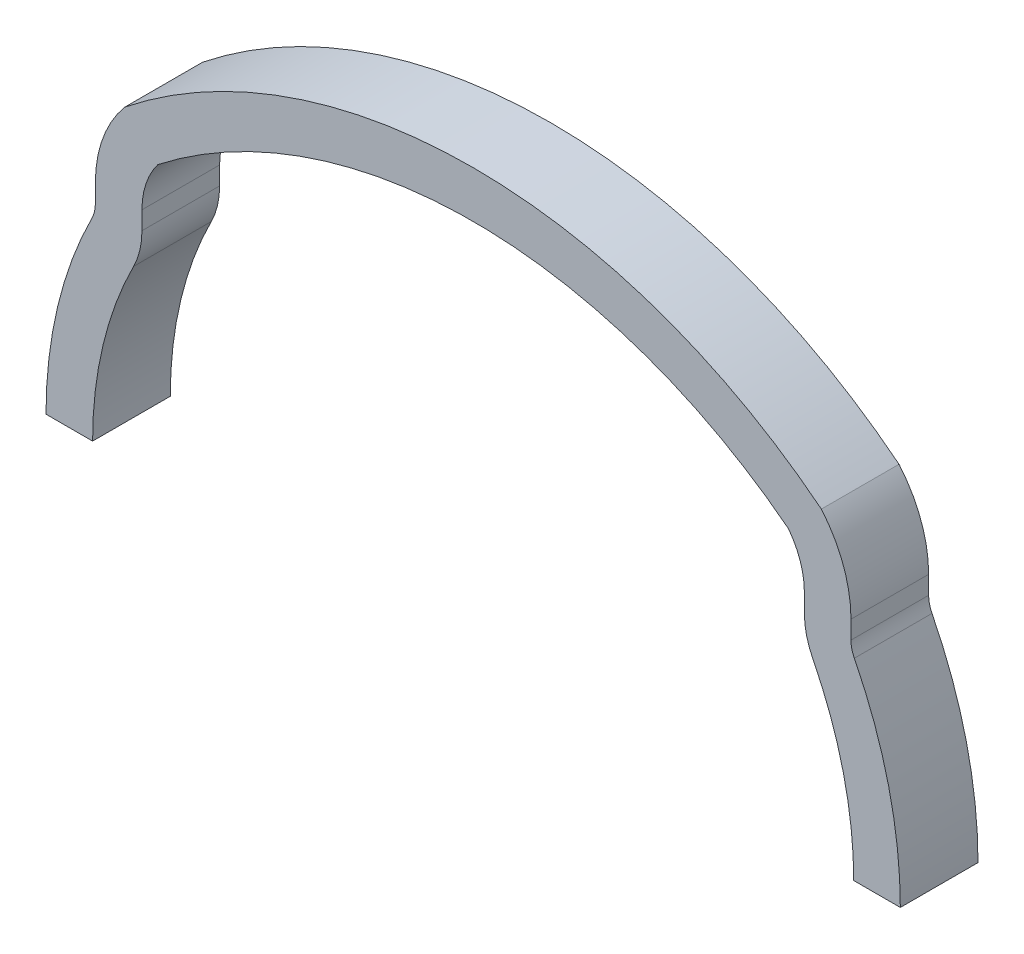
SolidWorks part; units mm, degrees
ref_plane "Front Plane" through (0, 0, 0) normal (0, 0, 1) x (1, 0, 0)
ref_plane "Top Plane" through (0, 0, 0) normal (0, 1, 0) x (1, 0, 0)
ref_plane "Right Plane" through (0, 0, 0) normal (1, 0, 0) x (0, 0, -1)
sketch "Sketch1" plane through (0, 0, 0) normal (0, 0, 1) x (1, 0, 0)
  line L1 (0, 0) -> (-38.2853, 0) construction
  line L2 (0, 0) -> (0, 65.2519) construction
  line L4 (-21, 16.3042) -> (-19.2879, 14.282) construction
  line L5 (-24.3231, 14.4853) -> (-24.3231, 13.3171)
  line L8 (-21.3231, 14.4853) -> (-21.3231, 13.3171)
  line L15 (-27.5, 0) -> (-24.5, 0)
  line L17 (27.5, 0) -> (24.5, 0)
  line L18 (24.3231, 14.4853) -> (24.3231, 13.3171)
  line L19 (21.3231, 14.4853) -> (21.3231, 13.3171)
  arc A9 (0, 24.5) -> (-20.2968, 17.52) centre (0, -8.5) ccw
  arc A10 (0, 24.5) -> (-21.3231, 16.6858) centre (0, -8.5) ccw construction
  arc A14 (0, 27.5) -> (-22.4159, 19.6697) centre (0, -8.5) ccw
  arc A15 (-22.4159, 19.6697) -> (-24.3231, 14.4853) centre (-16.3231, 14.4853) ccw
  arc A18 (-24.3231, 13.3171) -> (-24.5385, 12.4143) centre (-26.3231, 13.3171) cw
  arc A21 (-24.5385, 12.4143) -> (-27.5, 0) centre (0, 0) ccw
  arc A24 (21.8615, 11.06) -> (24.5, 0) centre (0, 0) cw
  arc A25 (-21.3231, 13.3171) -> (-21.8615, 11.06) centre (-26.3231, 13.3171) cw
  arc A26 (-20.2968, 17.52) -> (-21.3231, 14.4853) centre (-16.3231, 14.4853) ccw
  arc A27 (24.5385, 12.4143) -> (27.5, 0) centre (0, 0) cw
  arc A28 (0, 24) -> (-21, 16.3042) centre (0, -8.5) ccw construction
  arc A29 (24.3231, 13.3171) -> (24.5385, 12.4143) centre (26.3231, 13.3171) ccw
  arc A30 (0, 24) -> (-24, 0) centre (0, 0) ccw construction
  arc A31 (-21.8615, 11.06) -> (-24.5, 0) centre (0, 0) ccw
  arc A32 (21.3231, 13.3171) -> (21.8615, 11.06) centre (26.3231, 13.3171) ccw
  arc A33 (20.2968, 17.52) -> (21.3231, 14.4853) centre (16.3231, 14.4853) cw
  arc A34 (22.4159, 19.6697) -> (24.3231, 14.4853) centre (16.3231, 14.4853) cw
  arc A35 (0, 24.5) -> (20.2968, 17.52) centre (0, -8.5) cw
  arc A36 (0, 27.5) -> (22.4159, 19.6697) centre (0, -8.5) cw
  point P4 (0, 24)
  point P5 (0, 24)
  dimension "D1" = 3
  dimension "D2" = 65
  dimension "D7" = 48
  dimension "D5" = 0.5
  dimension "D3" = 21
extrude "Boss-Extrude1" add sketch "Sketch1" along normal blind 5
